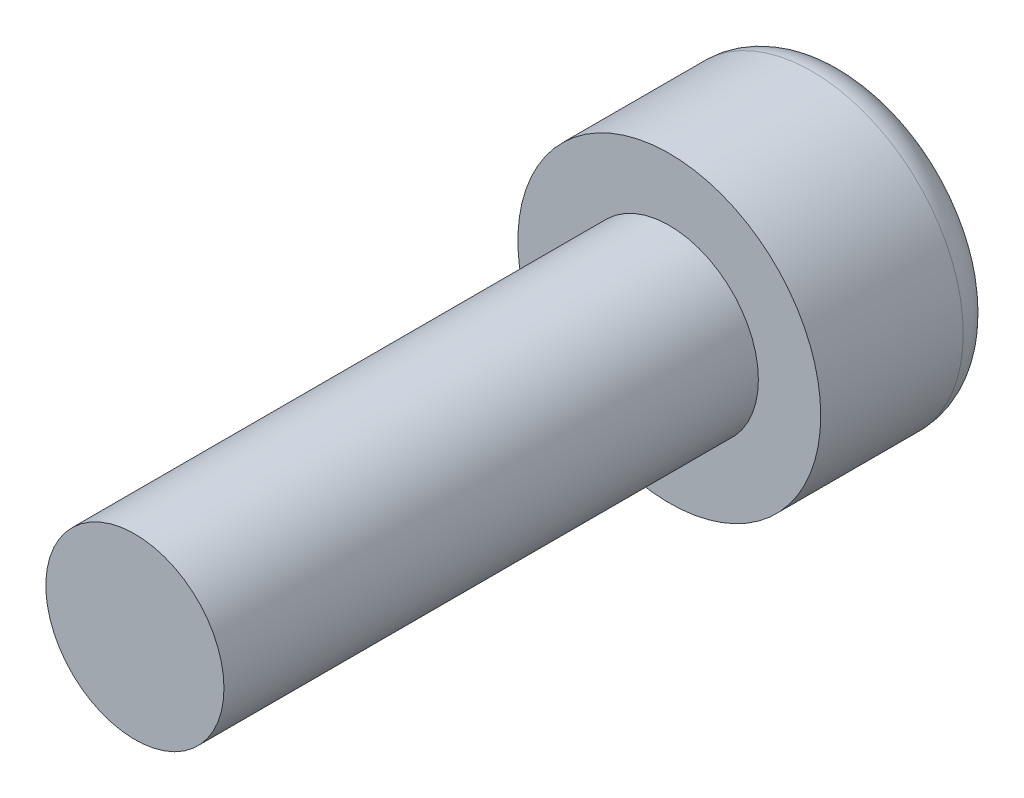
SolidWorks part; units mm, degrees
ref_plane "正面" through (0, 0, 0) normal (0, 0, 1) x (1, 0, 0)
ref_plane "平面" through (0, 0, 0) normal (0, 1, 0) x (1, 0, 0)
ref_plane "右側面" through (0, 0, 0) normal (1, 0, 0) x (0, 0, -1)
sketch "ｽｹｯﾁ1" plane through (0, 0, 0) normal (0, 0, 1) x (1, 0, 0)
  circle A0 centre (0, 0) radius 4.25
  dimension "D1" = 8.5
extrude "ﾎﾞｽ - 押し出し1" add sketch "ｽｹｯﾁ1" along normal blind 5
sketch "ｽｹｯﾁ2" plane through (0, 0, 5) normal (0, 0, 1) x (1, 0, 0)
  circle A0 centre (0, 0) radius 2.5
  dimension "D1" = 5
extrude "ﾎﾞｽ - 押し出し2" add sketch "ｽｹｯﾁ2" along normal blind 15
fillet "ﾌｨﾚｯﾄ1" radius 1 1 edges at (4.25, 0, 0)
